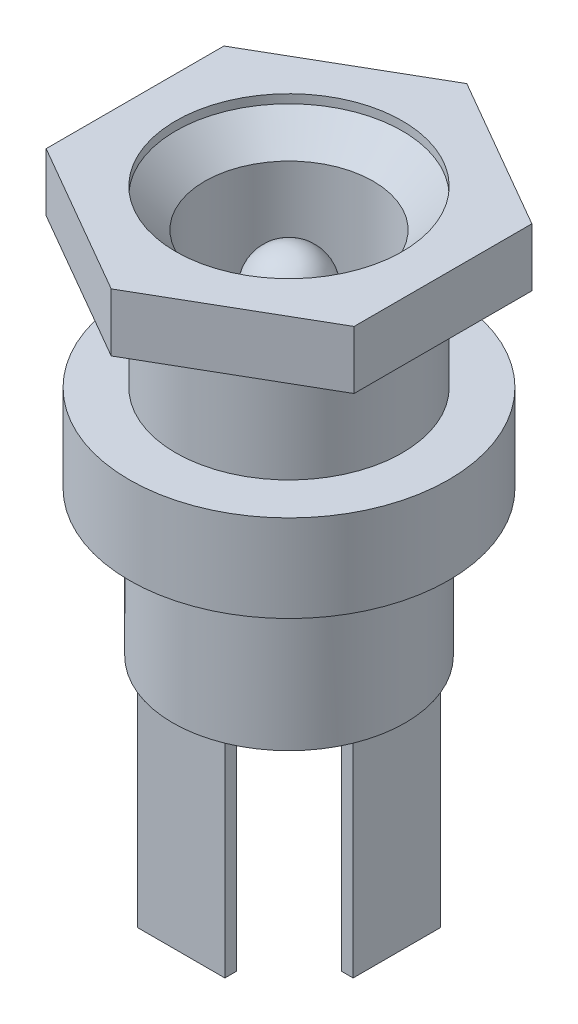
SolidWorks part; units mm, degrees
ref_plane "Front Plane" through (0, 0, 0) normal (0, 0, 1) x (1, 0, 0)
ref_plane "Top Plane" through (0, 0, 0) normal (0, 1, 0) x (1, 0, 0)
ref_plane "Right Plane" through (0, 0, 0) normal (1, 0, 0) x (0, 0, -1)
sketch "Sketch1" plane through (0, 0, 0) normal (1, 0, 0) x (0, 0, -1)
  line L2 (-3.9, 13.7) -> (-3.9, 8)
  line L3 (-3.9, 8) -> (-5.5, 8)
  line L4 (-5.5, 8) -> (-5.5, 5)
  line L5 (-5.5, 5) -> (-4, 5)
  line L6 (-4, 5) -> (-4, 0)
  line L7 (-4, 0) -> (0, 0)
  line L8 (-2.9, 12.7) -> (-2.9, 6.7)
  line L9 (-2.9, 6.7) -> (-1.25, 6.7)
  line L10 (-1.25, 6.7) -> (-1.25, 10.95)
  line L12 (0, 12.2) -> (0, 0)
  line L13 (-3.9, 13.7) -> (-2.9, 12.7)
  line L14 (0, 12.2) -> (-2.9, 12.2) construction
  arc A0 (0, 12.2) -> (-1.25, 10.95) centre (0, 10.95) ccw
  dimension "D1" = 3.9
  dimension "D2" = 1
  dimension "D3" = 1.25
  dimension "D4" = 5.7
  dimension "D5" = 3
  dimension "D6" = 5
  dimension "D7" = 5.5
  dimension "D8" = 4
  dimension "D9" = 6
  dimension "D10" = 1.5
  dimension "D11" = 45
revolve "Revolve1" add sketch "Sketch1" angle 360 about L12
sketch "Sketch2" plane through (0, 8, 0) normal (0, 1, 0) x (1, 0, 0)
  line L0 (0, 0) -> (0, 6.1199) construction
  line L1 (5.3, 3.06) -> (0, 6.1199)
  line L2 (0, 6.1199) -> (-5.3, 3.06)
  line L3 (-5.3, 3.06) -> (-5.3, -3.06)
  line L4 (-5.3, -3.06) -> (0, -6.1199)
  line L5 (0, -6.1199) -> (5.3, -3.06)
  line L6 (5.3, -3.06) -> (5.3, 3.06)
  circle A0 centre (0, 0) radius 5.3 construction
  circle A1 centre (0, 0) radius 3.9
  circle A2 centre (0, 0) radius 3.9 construction
  dimension "D1" = 10.6
extrude "Boss-Extrude1" add sketch "Sketch2" along normal blind 2 from offset 4
sketch "Sketch3" plane through (0, 0, 0) normal (0, -1, 0) x (1, 0, 0)
  line L0 (0, 0) -> (0, 3.3081) construction
  line L1 (-1.5, 3.7081) -> (1.5, 3.7081)
  line L2 (-1.5, 3.7081) -> (-1.5, 3.3081)
  line L3 (-1.5, 3.3081) -> (1.5, 3.3081)
  line L4 (1.5, 3.7081) -> (1.5, 3.3081)
  circle A0 centre (0, 0) radius 4 construction
  point P9 (1.5046, 3.7062)
  dimension "D1" = 3
  dimension "D2" = 0.4
extrude "Boss-Extrude2" add sketch "Sketch3" along normal blind 7
pattern_circular "CirPattern1" count 3 every 90 about axis through (0, 0, 0) along (0, 1, 0) of "Boss-Extrude2"
